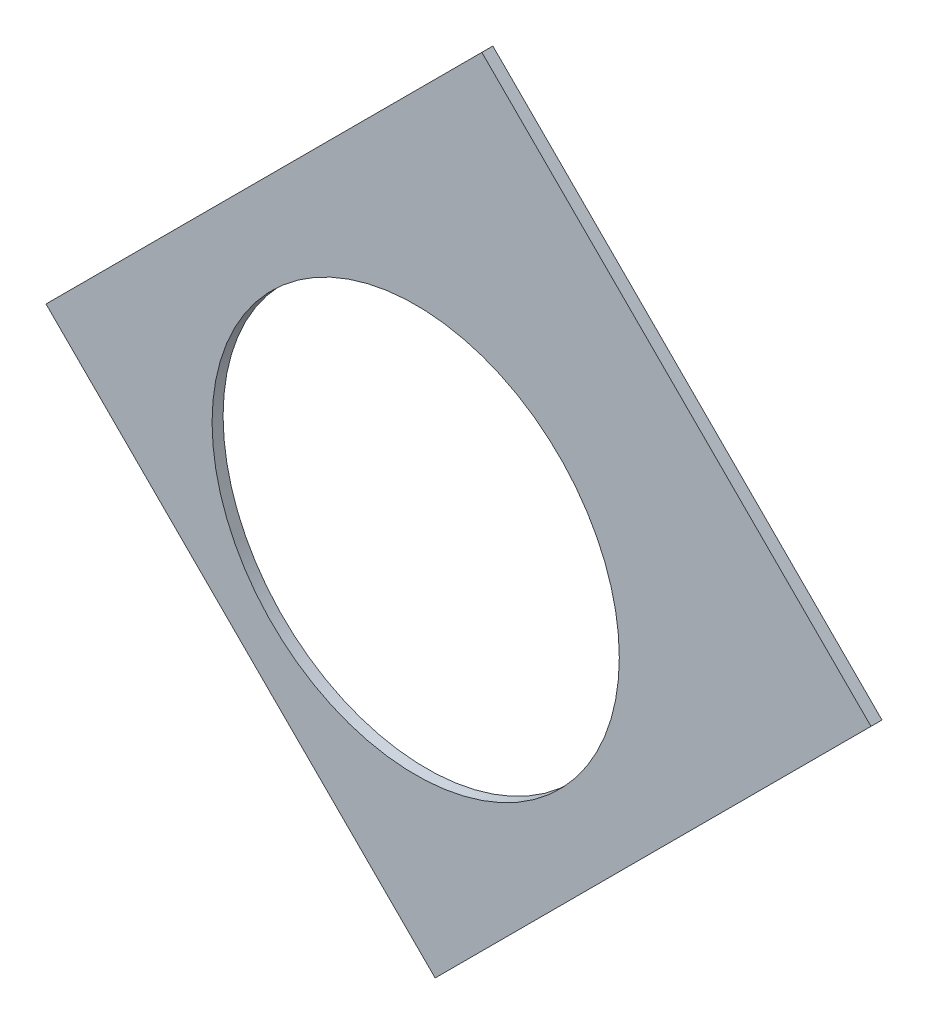
SolidWorks part; units mm, degrees
material "Copper"
ref_plane "Front Plane" through (0, 0, 0) normal (0, 0, 1) x (1, 0, 0)
ref_plane "Top Plane" through (0, 0, 0) normal (0, 1, 0) x (1, 0, 0)
ref_plane "Right Plane" through (0, 0, 0) normal (1, 0, 0) x (0, 0, -1)
sketch "Sketch1" plane through (0, 0, 0) normal (0, 0, 1) x (1, 0, 0)
  line L0 (0, 0) -> (320.3893, 0) construction
  line L1 (0, 0) -> (155.5285, 155.5285) construction
  line L2 (67.2115, 76.1917) -> (8.6967, 17.6769)
  line L3 (8.6967, 17.6769) -> (7.229, 14.1336)
  line L4 (101.4014, -6.35) -> (18.6489, -6.35)
  line L5 (15.1056, -4.8823) -> (18.6489, -6.35)
  line L6 (88.6729, 6.35) -> (27.8605, 6.35)
  line L9 (67.1914, 58.2111) -> (24.1905, 15.2102)
  line L10 (0, 0) -> (40.4486, 97.6516) construction
  line L11 (0, 0) -> (123.4567, -51.1374) construction
  line L18 (8.6967, 17.6769) -> (13.294, 8.6183) construction
  line L19 (18.6489, -6.35) -> (15.4943, 3.3063) construction
  line L20 (27.8605, 6.35) -> (27.7442, 6.7059) construction
  line L21 (24.1905, 15.2102) -> (24.3599, 14.8764) construction
  arc A0 (7.229, 14.1336) -> (15.1056, -4.8823) centre (0, 0) cw
  arc A1 (67.2115, 76.1917) -> (101.4014, -6.35) centre (0, 0) cw
  arc A2 (24.1905, 15.2102) -> (27.8605, 6.35) centre (0, 0) cw
  arc A3 (67.1914, 58.2111) -> (88.6729, 6.35) centre (0, 0) cw
  arc A8 (13.294, 8.6183) -> (15.4943, 3.3063) centre (0, 0) cw construction
  arc A9 (24.3599, 14.8764) -> (27.7442, 6.7059) centre (0, 0) cw construction
  dimension "D1" = 45
  dimension "D3" = 6.35
  dimension "D4" = 15.875
  dimension "D7" = 22.5
  dimension "D8" = 101.6
  dimension "D11" = 12.7
  dimension "D12" = 12.7
  dimension "D2" = 6.35
  dimension "D5" = 67.5
  dimension "D9" = 1.27
  dimension "D10" = 1.27
  dimension "D6" = 12.7
extrude "Boss-Extrude1" add sketch "Sketch1" along normal blind 0.254
sketch "Sketch2" plane through (0, 0, 0.254) normal (0, 0, 1) x (1, 0, 0)
  line L0 (0, 0) -> (101.6, 0) construction
  line L1 (0, 0) -> (71.842, 71.842) construction
  line L3 (0, 0) -> (22.225, 0) construction
  line L4 (0, 0) -> (15.7154, 15.7154) construction
  line L5 (0, 0) -> (95.25, 0) construction
  line L6 (0, 0) -> (92.0044, 24.6525) construction
  arc A0 (101.4014, -6.35) -> (67.2115, 76.1917) centre (0, 0) ccw construction
  circle A1 centre (22.225, 0) radius 4.699
  arc A2 (15.1056, -4.8823) -> (7.229, 14.1336) centre (0, 0) ccw construction
  circle A3 centre (36.195, 0) radius 4.699
  circle A4 centre (61.722, 0) radius 4.699
  circle A5 centre (75.692, 0) radius 4.699
  circle A6 centre (95.25, 0) radius 4.699
  circle A7 centre (15.7154, 15.7154) radius 4.699
  circle A8 centre (25.5937, 25.5937) radius 4.699
  circle A9 centre (43.644, 43.644) radius 4.699
  circle A10 centre (53.5223, 53.5223) radius 4.699
  circle A11 centre (92.0044, 24.6525) radius 4.699
  circle A12 centre (82.4889, 47.625) radius 4.699
  circle A13 centre (67.3519, 67.3519) radius 4.699
  dimension "D3" = 9.398
  dimension "D1" = 45
  dimension "D2" = 6.35
  dimension "D4" = 6.35
  dimension "D5" = 13.97
  dimension "D7" = 13.97
  dimension "D8" = 19.558
  dimension "D9" = 45
  dimension "D10" = 15
  dimension "D11" = 25.527
  dimension "D6" = 2
extrude "Cut-Extrude1" cut sketch "Sketch2" against normal through all
sketch "Sketch3" plane through (0, 0, 0.254) normal (0, 0, 1) x (1, 0, 0)
  line L0 (15.2664, 24.2467) -> (17.0625, 26.0427)
  line L1 (15.2664, 24.2467) -> (15.7154, 23.7977)
  line L2 (17.0625, 26.0427) -> (17.5115, 25.5937)
  line L3 (15.7154, 23.7977) -> (17.5115, 25.5937)
  line L4 (67.2115, 76.1917) -> (8.6967, 17.6769) construction
  line L5 (44.9911, 53.9713) -> (43.195, 52.1753)
  line L6 (44.9911, 53.9713) -> (45.4401, 53.5223)
  line L7 (43.195, 52.1753) -> (43.644, 51.7263)
  line L8 (45.4401, 53.5223) -> (43.644, 51.7263)
  line L9 (27.94, -6.35) -> (30.48, -6.35)
  line L10 (27.94, -6.35) -> (27.94, -5.715)
  line L11 (30.48, -6.35) -> (30.48, -5.715)
  line L12 (27.94, -5.715) -> (30.48, -5.715)
  line L13 (18.6489, -6.35) -> (101.4014, -6.35) construction
  line L14 (67.437, -6.35) -> (69.977, -6.35)
  line L15 (67.437, -6.35) -> (67.437, -5.715)
  line L16 (69.977, -6.35) -> (69.977, -5.715)
  line L17 (67.437, -5.715) -> (69.977, -5.715)
  line L18 (29.2307, 38.211) -> (31.0268, 40.007)
  line L19 (29.2307, 38.211) -> (29.6797, 37.762)
  line L20 (31.0268, 40.007) -> (31.4758, 39.558)
  line L21 (29.6797, 37.762) -> (31.4758, 39.558)
  line L22 (56.845, 65.8253) -> (55.049, 64.0292)
  line L23 (56.845, 65.8253) -> (57.294, 65.3763)
  line L24 (55.049, 64.0292) -> (55.498, 63.5802)
  line L25 (57.294, 65.3763) -> (55.498, 63.5802)
  line L26 (47.6885, -6.35) -> (50.2285, -6.35)
  line L27 (47.6885, -6.35) -> (47.6885, -5.715)
  line L28 (50.2285, -6.35) -> (50.2285, -5.715)
  line L29 (47.6885, -5.715) -> (50.2285, -5.715)
  line L30 (84.201, -6.35) -> (86.741, -6.35)
  line L31 (84.201, -6.35) -> (84.201, -5.715)
  line L32 (86.741, -6.35) -> (86.741, -5.715)
  line L33 (84.201, -5.715) -> (86.741, -5.715)
  line L34 (0, 0) -> (100.7308, 13.2615) construction
  line L35 (0, 0) -> (93.8662, 38.8806) construction
  line L36 (0, 0) -> (80.6047, 61.8502) construction
  line L37 (0, 0) -> (101.6, 0) construction
  line L38 (99.9355, 14.4377) -> (100.267, 11.9194)
  line L39 (99.9355, 14.4377) -> (101.1946, 14.6035)
  line L40 (100.267, 11.9194) -> (101.5261, 12.0852)
  line L41 (101.1946, 14.6035) -> (101.5261, 12.0852)
  line L42 (99.9355, 14.4377) -> (101.5261, 12.0852) construction
  line L43 (100.267, 11.9194) -> (101.1946, 14.6035) construction
  line L44 (93.7655, 37.4643) -> (94.9388, 37.9503)
  line L45 (93.7655, 37.4643) -> (92.7935, 39.811)
  line L46 (94.9388, 37.9503) -> (93.9668, 40.297)
  line L47 (92.7935, 39.811) -> (93.9668, 40.297)
  line L48 (93.7655, 37.4643) -> (93.9668, 40.297) construction
  line L49 (94.9388, 37.9503) -> (92.7935, 39.811) construction
  line L50 (79.3278, 62.4712) -> (80.874, 60.456)
  line L51 (79.3278, 62.4712) -> (80.3354, 63.2443)
  line L52 (80.874, 60.456) -> (81.8816, 61.2292)
  line L53 (80.3354, 63.2443) -> (81.8816, 61.2292)
  line L54 (79.3278, 62.4712) -> (81.8816, 61.2292) construction
  line L55 (80.874, 60.456) -> (80.3354, 63.2443) construction
  line L56 (13.5939, 7.0054) -> (14.5659, 4.6588)
  line L57 (13.5939, 7.0054) -> (14.7672, 7.4914)
  line L58 (14.5659, 4.6588) -> (15.7393, 5.1448)
  line L59 (14.7672, 7.4914) -> (15.7393, 5.1448)
  line L60 (13.5939, 7.0054) -> (15.7393, 5.1448) construction
  line L61 (14.5659, 4.6588) -> (14.7672, 7.4914) construction
  circle A0 centre (15.7154, 15.7154) radius 4.699 construction
  circle A1 centre (43.644, 43.644) radius 4.699 construction
  circle A2 centre (22.225, 0) radius 4.699 construction
  circle A3 centre (61.722, 0) radius 4.699 construction
  arc A4 (101.4014, -6.35) -> (67.2115, 76.1917) centre (0, 0) ccw construction
  arc A9 (15.1056, -4.8823) -> (7.229, 14.1336) centre (0, 0) ccw construction
  circle A10 centre (36.195, 0) radius 4.699 construction
  circle A11 centre (75.692, 0) radius 4.699 construction
  circle A12 centre (25.5937, 25.5937) radius 4.699 construction
  circle A13 centre (53.5223, 53.5223) radius 4.699 construction
  point P75 (14.6666, 6.0751)
  dimension "D2" = 5.715
  dimension "D3" = 2.54
  dimension "D6" = 5.715
  dimension "D8" = 0.635
  dimension "D9" = 5.715
  dimension "D12" = 5.715
  dimension "D4" = 7.5
  dimension "D5" = 22.5
  dimension "D7" = 37.5
  dimension "D10" = 90
  dimension "D11" = 1.27
  dimension "D14" = 0.635
  dimension "D15" = 90
  dimension "D18" = 0.635
  dimension "D19" = 90
  dimension "D22" = 0.635
  dimension "D20" = 1.27
  dimension "D17" = 0.635
  dimension "D13" = 11.4935
  dimension "D16" = 8.509
  dimension "D21" = 11.4935
  dimension "D23" = 8.509
extrude "Cut-Extrude2" cut sketch "Sketch3" against normal through all
sketch "Sketch5" plane through (0, 0, 0.254) normal (0, 0, 1) x (1, 0, 0)
  line L0 (53.9713, 44.9911) -> (64.0292, 55.049)
  line L1 (53.9713, 44.9911) -> (44.9911, 53.9713)
  line L2 (64.0292, 55.049) -> (55.049, 64.0292)
  line L3 (57.294, 65.3763) -> (56.845, 65.8253) construction
  line L4 (44.9911, 53.9713) -> (55.049, 64.0292)
  line L5 (67.1914, 58.2111) -> (24.1905, 15.2102) construction
  line L9 (43.195, 52.1753) -> (43.644, 51.7263) construction
  dimension "D1" = 2.54
  dimension "D2" = 2.54
extrude "Cut-Extrude5" cut sketch "Sketch5" against normal through all flip side to cut
equation "\"cSep\"= 1.005"
equation "\"D11@Sketch2\"=\"cSep\""
equation "\"cSep2\"= \"D8@Sketch2\""
equation "\"D13@Sketch3\"=\"cSep\"/2-.05"
equation "\"D16@Sketch3\"=\"cSep2\"/2-.05"
equation "\"D21@Sketch3\"=\"cSep\"/2-.05"
equation "\"D23@Sketch3\"=\"cSep2\"/2-.05"
